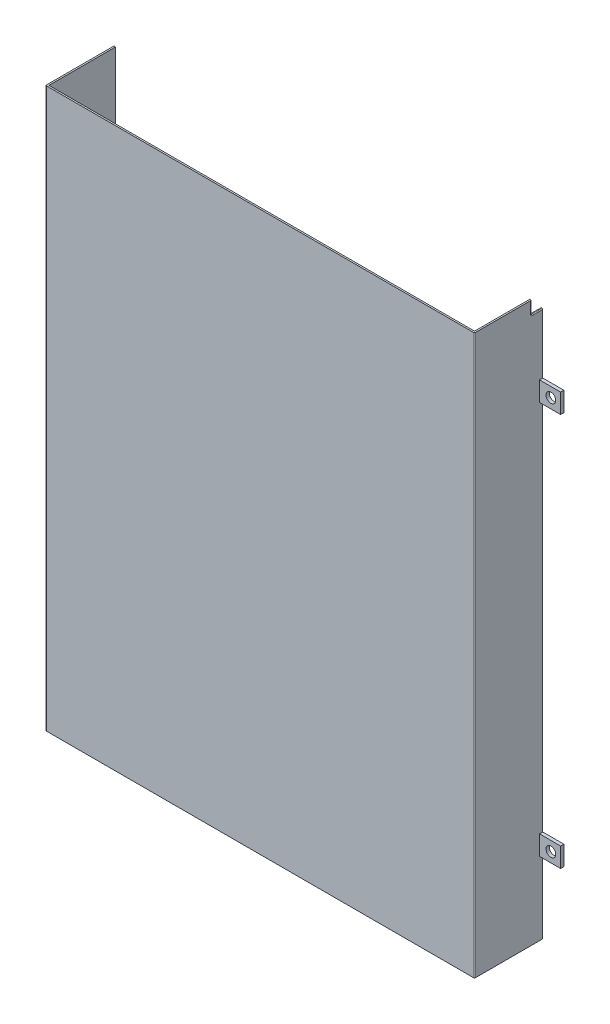
SolidWorks part; units mm, degrees
material "6061-O (SS)"
ref_plane "Płaszczyzna XY" through (0, 0, 0) normal (0, 0, 1) x (1, 0, 0)
ref_plane "Płaszczyzna XZ" through (0, 0, 0) normal (0, 1, 0) x (1, 0, 0)
ref_plane "Płaszczyzna YZ" through (0, 0, 0) normal (1, 0, 0) x (0, 0, -1)
sketch "Szkic1" plane through (0, 0, 0) normal (0, 1, 0) x (1, 0, 0)
  line L0 (211, -111) -> (211, -152)
  line L1 (211, -152) -> (-51, -152)
  line L2 (-51, -152) -> (-51, -111)
  dimension "D2" = 41
  dimension "D1" = 262
  dimension "D3" = 41
  dimension "D4" = 211
  dimension "D5" = 152
extrude "Wyciągnięcie-cienka ścianka1" add sketch "Szkic1" along normal blind 172 and the other way blind 172 thin thin type one direction reverse wall 1
ref_plane "Płaszczyzna1" through (0, 0, 111) normal (0, 0, -1) x (-1, 0, 0)
sketch "Szkic2" plane through (0, 0, 111) normal (0, 0, -1) x (-1, 0, 0)
  line L8 (-212, -127) -> (-225, -127)
  line L9 (-212, -127) -> (-212, -115)
  line L10 (-212, -115) -> (-225, -115)
  line L11 (-225, -127) -> (-225, -115)
  line L12 (-212, 115) -> (-225, 115)
  line L13 (-212, 115) -> (-212, 127)
  line L14 (-212, 127) -> (-225, 127)
  line L15 (-225, 115) -> (-225, 127)
  line L17 (-212, -172) -> (-212, 172) construction
  circle A2 centre (-219, -121) radius 3
  circle A3 centre (-219, 121) radius 3
  dimension "D19" = 6
  dimension "D22" = 6
  dimension "D5" = 13
  dimension "D6" = 12
  dimension "D7" = 13
  dimension "D8" = 12
  dimension "D9" = 45
  dimension "D10" = 45
  dimension "D20" = 6
  dimension "D21" = 6
  dimension "D23" = 6
  dimension "D24" = 6
extrude "Dodanie-wyciągnięcie1" add sketch "Szkic2" against normal blind 2
fillet "Zaokrąglenie1" radius 0.5 2 edges at (212, 0, 153) (-52, 0, 153)
ref_plane "Płaszczyzna2" through (212, 0, 0) normal (1, 0, 0) x (0, 0, -1)
sketch "Szkic5" plane through (212, 0, 0) normal (1, 0, 0) x (0, 0, -1)
  line L0 (-118, 172) -> (-118, 164)
  line L1 (-111, 172) -> (-152.5, 172) construction
  line L2 (-118, 164) -> (-111, 164)
  line L3 (-111, 127) -> (-111, 172) construction
  dimension "D1" = 8
  dimension "D2" = 7
extrude "Wytnij-wyciągnięcie2" cut sketch "Szkic5" against normal blind 2 and the other way through all
fillet "Zaokrąglenie4" radius 0.5 1 edges at (211.5, 164, 118)
fillet "Zaokrąglenie5" radius 0.5 3 edges at (212, 164.1464, 117.8536) (212, 168.25, 118) (212, 164, 114.25)
